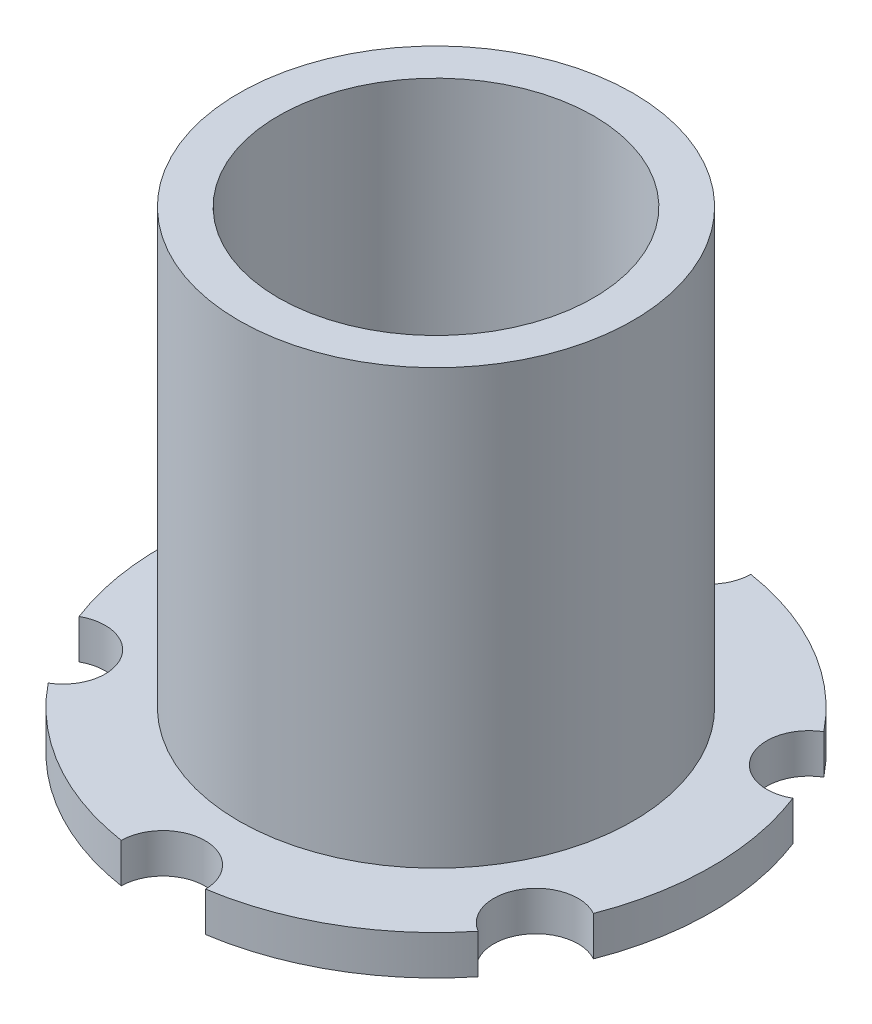
SolidWorks part; units mm, degrees
ref_plane "Front" through (0, 0, 0) normal (0, 0, 1) x (1, 0, 0)
ref_plane "Top" through (0, 0, 0) normal (0, 1, 0) x (1, 0, 0)
ref_plane "Right" through (0, 0, 0) normal (1, 0, 0) x (0, 0, -1)
sketch "Sketch1" plane through (0, 0, 0) normal (0, 1, 0) x (1, 0, 0)
  circle A0 centre (0, 0) radius 6.35
  circle A1 centre (0, 0) radius 7.9375
  circle A2 centre (0, 0) radius 11.1125
  dimension "ID" = 12.7
  dimension "OD" = 15.875
  dimension "FlangeOD" = 22.225
sketch "Sketch2" plane through (0, 0, 0) normal (0, 1, 0) x (1, 0, 0)
  circle A0 centre (0, 0) radius 6.35 construction
  circle A1 centre (0, 0) radius 7.9375 construction
  circle A2 centre (0, 0) radius 6.35
  circle A3 centre (0, 0) radius 7.9375
extrude "Boss-Extrude1" add sketch "Sketch2" along normal blind 19.05
sketch "Sketch3" plane through (0, 0, 0) normal (0, 1, 0) x (1, 0, 0)
  circle A0 centre (0, 0) radius 11.1125 construction
  circle A1 centre (0, 0) radius 7.9375 construction
  circle A2 centre (0, 0) radius 11.1125
  circle A3 centre (0, 0) radius 7.9375
extrude "Boss-Extrude2" add sketch "Sketch3" along normal blind 1.5875
hole_wizard "M3 Clearance Hole1" positions "Sketch4" profile "Sketch5" hole size "M3" standard "ANSI Metric" end condition through all
sketch "Sketch4" plane through (0, 0, 0) normal (0, -1, 0) x (-1, 0, 0)
  point P0 (0, -11)
  point P4 (0, 0)
  dimension "D1" = 11
sketch "Sketch5" plane through (0, 0, 11) normal (1, 0, 0) x (0, 0, -1)
  line L0 (0, 0) -> (0, 19.05)
  line L1 (0, 19.05) -> (1.7, 19.05)
  line L2 (1.7, 19.05) -> (1.7, 0)
  line L5 (1.7, 0) -> (0, 0)
  line L11 (0, -6.35) -> (0, 107.95) construction
  dimension "Thru Hole Dia." = 3.4
  dimension "Thru Hole Depth" = 19.05
pattern_circular "CirPattern1" count 6 every 60 about axis through (0, 0, 0) along (0, 1, 0) of "M3 Clearance Hole1"
